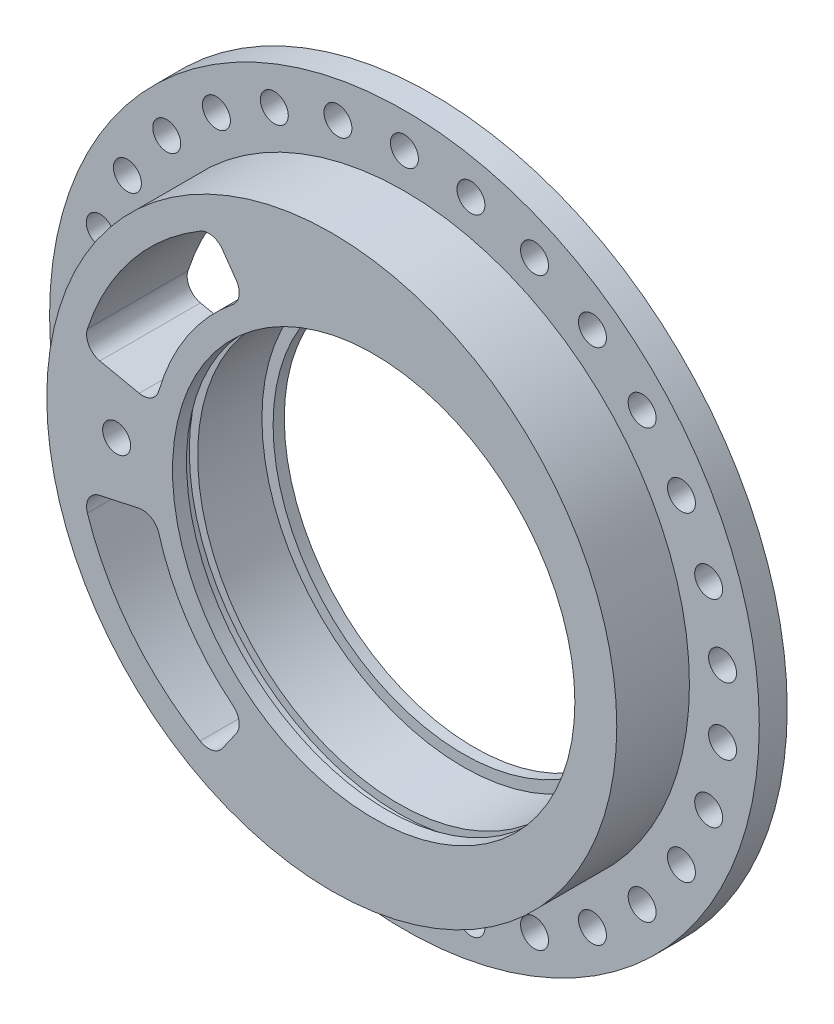
SolidWorks part; units mm, degrees
ref_plane "Front Plane" through (0, 0, 0) normal (0, 0, 1) x (1, 0, 0)
ref_plane "Top Plane" through (0, 0, 0) normal (0, 1, 0) x (1, 0, 0)
ref_plane "Right Plane" through (0, 0, 0) normal (1, 0, 0) x (0, 0, -1)
sketch "Sketch1" plane through (0, 0, 0) normal (0, 0, 1) x (1, 0, 0)
  circle A0 centre (0, 0) radius 63.5
  dimension "D1" = 127
extrude "Boss-Extrude1" add sketch "Sketch1" along normal blind 5
sketch "Sketch2" plane through (0, 0, 5) normal (0, 0, 1) x (1, 0, 0)
  circle A0 centre (0, 0) radius 51
  dimension "D1" = 102
extrude "Boss-Extrude2" add sketch "Sketch2" along normal blind 13
sketch "Sketch3" plane through (0, 0, 18) normal (0, 0, 1) x (1, 0, 0)
  line L0 (0, 0) -> (7.5, 0)
  circle A0 centre (7.5, 0) radius 36
  dimension "D2" = 72
  dimension "D1" = 7.5
extrude "Cut-Extrude1" cut sketch "Sketch3" against normal through all
sketch "Sketch4" plane through (0, 0, 18) normal (0, 0, 1) x (1, 0, 0)
  circle A0 centre (7.5, 0) radius 37.5
  circle A1 centre (7.5, 0) radius 36
  dimension "D1" = 75
  dimension "D2" = 72
extrude "Cut-Extrude3" cut sketch "Sketch4" against normal blind 2 from offset 2.5 offset against normal yes
sketch "Sketch6" plane through (0, 0, 0) normal (0, 0, -1) x (-1, 0, 0)
  circle A0 centre (-7.5, 0) radius 34
  circle A2 centre (-7.5, 0) radius 36
  dimension "D1" = 68
extrude "Boss-Extrude6" add sketch "Sketch6" against normal blind 2
sketch "Sketch9" plane through (0, 0, 5) normal (0, 0, 1) x (1, 0, 0)
  circle A1 centre (0, 57.24) radius 2.5
  circle A2 centre (11.9009, 55.9892) radius 2.5
  circle A3 centre (23.2816, 52.2913) radius 2.5
  circle A4 centre (33.6448, 46.3081) radius 2.5
  circle A5 centre (42.5376, 38.301) radius 2.5
  circle A6 centre (49.5713, 28.62) radius 2.5
  circle A7 centre (54.4385, 17.6881) radius 2.5
  circle A8 centre (56.9264, 5.9832) radius 2.5
  circle A9 centre (56.9264, -5.9832) radius 2.5
  circle A10 centre (54.4385, -17.6881) radius 2.5
  circle A11 centre (49.5713, -28.62) radius 2.5
  circle A12 centre (42.5376, -38.301) radius 2.5
  circle A13 centre (33.6448, -46.3081) radius 2.5
  circle A14 centre (23.2816, -52.2913) radius 2.5
  circle A15 centre (11.9009, -55.9892) radius 2.5
  circle A16 centre (0, -57.24) radius 2.5
  circle A17 centre (-11.9009, -55.9892) radius 2.5
  circle A18 centre (-23.2816, -52.2913) radius 2.5
  circle A19 centre (-33.6448, -46.3081) radius 2.5
  circle A20 centre (-42.5376, -38.301) radius 2.5
  circle A21 centre (-49.5713, -28.62) radius 2.5
  circle A22 centre (-54.4385, -17.6881) radius 2.5
  circle A23 centre (-56.9264, -5.9832) radius 2.5
  circle A24 centre (-56.9264, 5.9832) radius 2.5
  circle A25 centre (-54.4385, 17.6881) radius 2.5
  circle A26 centre (-49.5713, 28.62) radius 2.5
  circle A27 centre (-42.5376, 38.301) radius 2.5
  circle A28 centre (-33.6448, 46.3081) radius 2.5
  circle A29 centre (-23.2816, 52.2913) radius 2.5
  circle A30 centre (-11.9009, 55.9892) radius 2.5
  dimension "D2" = 5
  dimension "D3" = 30
extrude "Cut-Extrude9" cut sketch "Sketch9" against normal through all
sketch "Sketch10" plane through (0, 0, 18) normal (0, 0, 1) x (1, 0, 0)
  circle A0 centre (-38.5, 0) radius 2.5
  circle A1 centre (7.5, 0) radius 36 construction
  dimension "D2" = 5
  dimension "D1" = 46
extrude "Cut-Extrude10" cut sketch "Sketch10" against normal through all
sketch "Sketch11" plane through (0, 0, 18) normal (0, 0, 1) x (1, 0, 0)
  line L0 (-15.4431, 32.7661) -> (-21.1156, 40.8673)
  line L1 (-31.6259, 8.3165) -> (-44.6447, 11.0837)
  line L2 (7.5, 0) -> (-94.6784, 0)
  arc A0 (-21.1156, 40.8673) -> (-44.6447, 11.0837) centre (0, 0) ccw
  arc A1 (-15.4431, 32.7661) -> (-31.6259, 8.3165) centre (7.5, 0) ccw
  dimension "D1" = 80
  dimension "D2" = 92
  dimension "D3" = 12
  dimension "D4" = 55
extrude "Cut-Extrude11" cut sketch "Sketch11" against normal through all contours A1 L0 A0 L1
mirror "Mirror1" about plane through (0, 0, 0) normal (0, 1, 0) of "Cut-Extrude11"
fillet "Fillet1" radius 3 1 edges at (-44.6447, 11.0837, 9)
fillet "Fillet2" radius 3 3 edges at (-21.1156, 40.8673, 9) (-15.4431, 32.7661, 9) (-31.6259, 8.3165, 9)
fillet "Fillet3" radius 3 4 edges at (-21.1156, -40.8673, 9) (-15.4431, -32.7661, 9) (-31.6259, -8.3165, 9) (-44.6447, -11.0837, 9)
